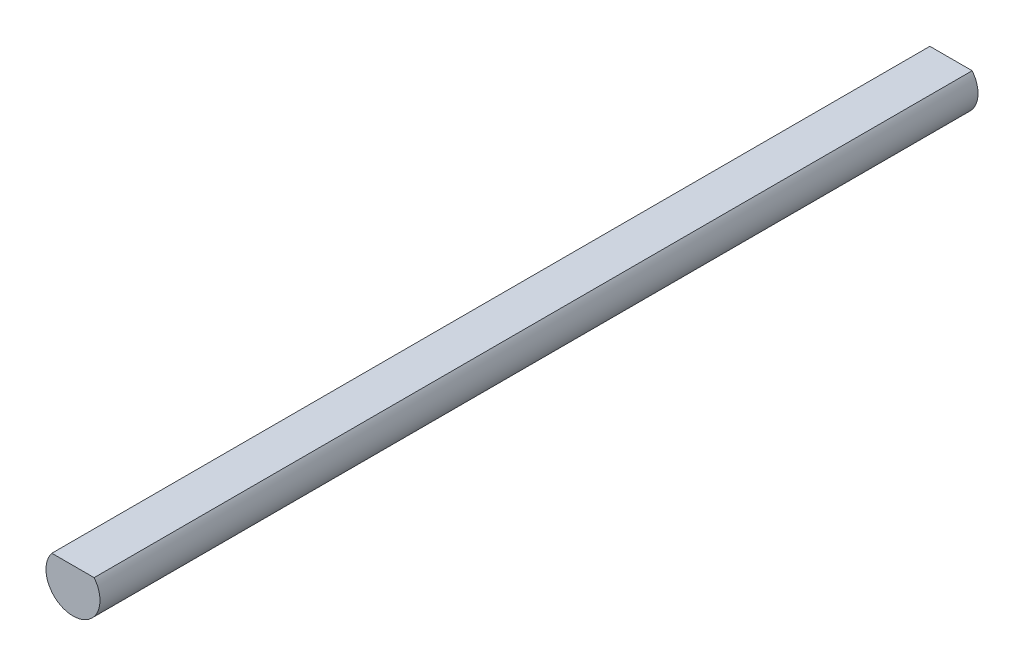
SolidWorks part; units mm, degrees
ref_plane "Front Plane" through (0, 0, 0) normal (0, 0, 1) x (1, 0, 0)
ref_plane "Top Plane" through (0, 0, 0) normal (0, 1, 0) x (1, 0, 0)
ref_plane "Right Plane" through (0, 0, 0) normal (1, 0, 0) x (0, 0, -1)
sketch "Sketch2" plane through (0, 0, 0) normal (0, 0, 1) x (1, 0, 0)
  circle A0 centre (0, 0) radius 4
  dimension "D1" = 8
extrude "Boss-Extrude1" add sketch "Sketch2" along normal blind 130
sketch "Sketch3" plane through (0, 0, 130) normal (0, 0, 1) x (1, 0, 0)
  line L0 (-3.131, 2.4893) -> (3.131, 2.4893)
  circle A0 centre (0, 0) radius 4 construction
  arc A1 (-3.131, 2.4893) -> (3.131, 2.4893) centre (0, 0) cw
extrude "Cut-Extrude1" cut sketch "Sketch3" against normal through all both and the other way through all
